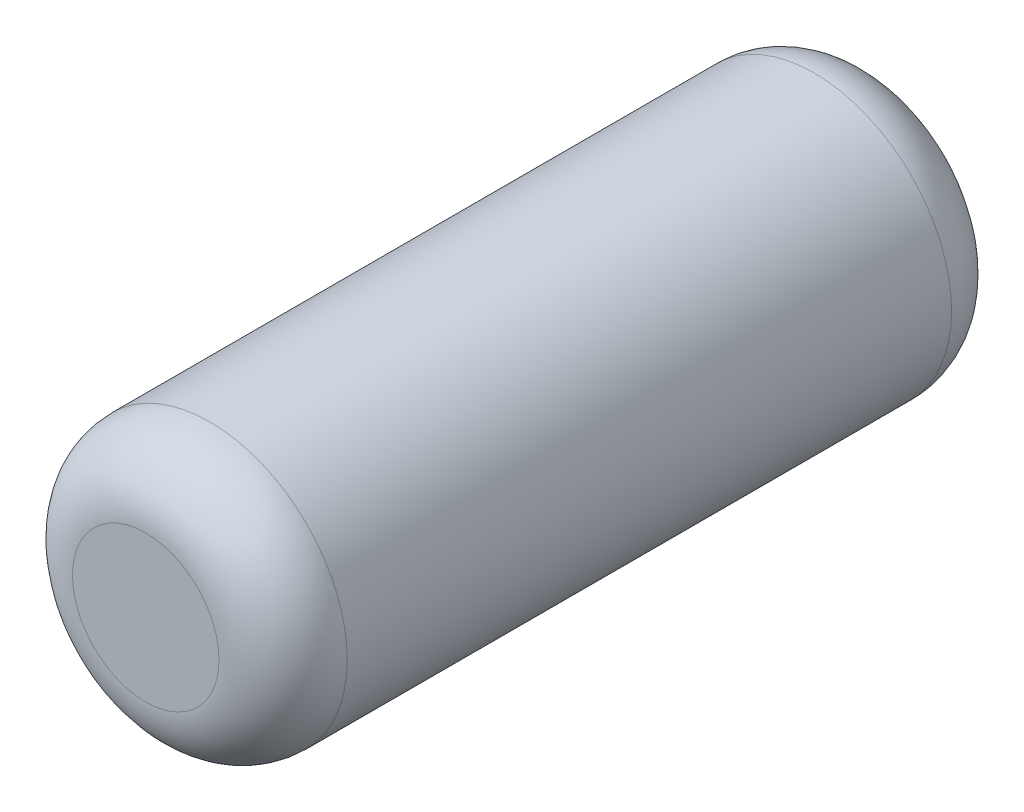
SolidWorks part; units mm, degrees
ref_plane "Front" through (0, 0, 0) normal (0, 0, 1) x (1, 0, 0)
ref_plane "Top" through (0, 0, 0) normal (0, 1, 0) x (1, 0, 0)
ref_plane "Right" through (0, 0, 0) normal (1, 0, 0) x (0, 0, -1)
sketch "Sketch1" plane through (0, 0, 0) normal (0, 0, 1) x (1, 0, 0)
  circle A0 centre (0, 0) radius 0.75
  dimension "D1" = 1.5
extrude "Boss-Extrude1" add sketch "Sketch1" along normal mid plane 4
fillet "Fillet1" radius 0.35 2 edges at (0.75, 0, -2) (0.75, 0, 2)
